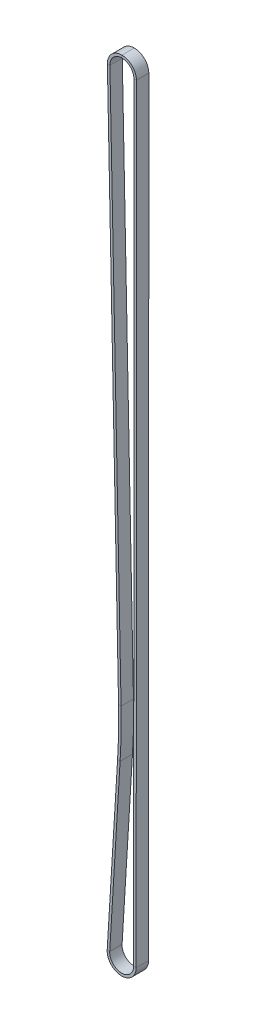
SolidWorks part; units mm, degrees
ref_plane "Front Plane" through (0, 0, 0) normal (0, 0, 1) x (1, 0, 0)
ref_plane "Top Plane" through (0, 0, 0) normal (0, 1, 0) x (1, 0, 0)
ref_plane "Right Plane" through (0, 0, 0) normal (1, 0, 0) x (0, 0, -1)
sketch "Sketch2" plane through (0, 0, 0) normal (0, 0, 1) x (1, 0, 0)
  line L0 (0, 0) -> (1, 0) construction
  line L1 (0, 0) -> (0, 1) construction
  line L3 (7.0911, -457.202) -> (7.2181, -0.002)
  line L4 (-7.2166, -0.1467) -> (-0.574, -326.9723)
  line L5 (-1.1583, -355.6925) -> (-7.3316, -456.7599)
  arc A0 (7.2181, -0.002) -> (-7.2166, -0.1467) centre (0, 0) ccw
  arc A1 (-7.3316, -456.7599) -> (7.0911, -457.202) centre (-0.127, -457.2) ccw
  arc A2 (-0.574, -326.9723) -> (-1.1583, -355.6925) centre (-353.8135, -334.1517) cw
sketch "Sketch3" plane through (0, 0, 0) normal (1, 0, 0) x (0, 0, -1)
  line L0 (0, 7.2181) -> (0, -0.1467) construction
  line L1 (0, 8.6371) -> (7.366, 8.6371)
  line L2 (0, 8.6371) -> (0, 7.1371)
  line L3 (0, 7.1371) -> (7.366, 7.1371)
  line L4 (7.366, 8.6371) -> (7.366, 7.1371)
  dimension "D1" = 1.5
  dimension "D2" = 7.366
sweep "Sweep1" add profiles "Sketch3" path "Sketch2"
